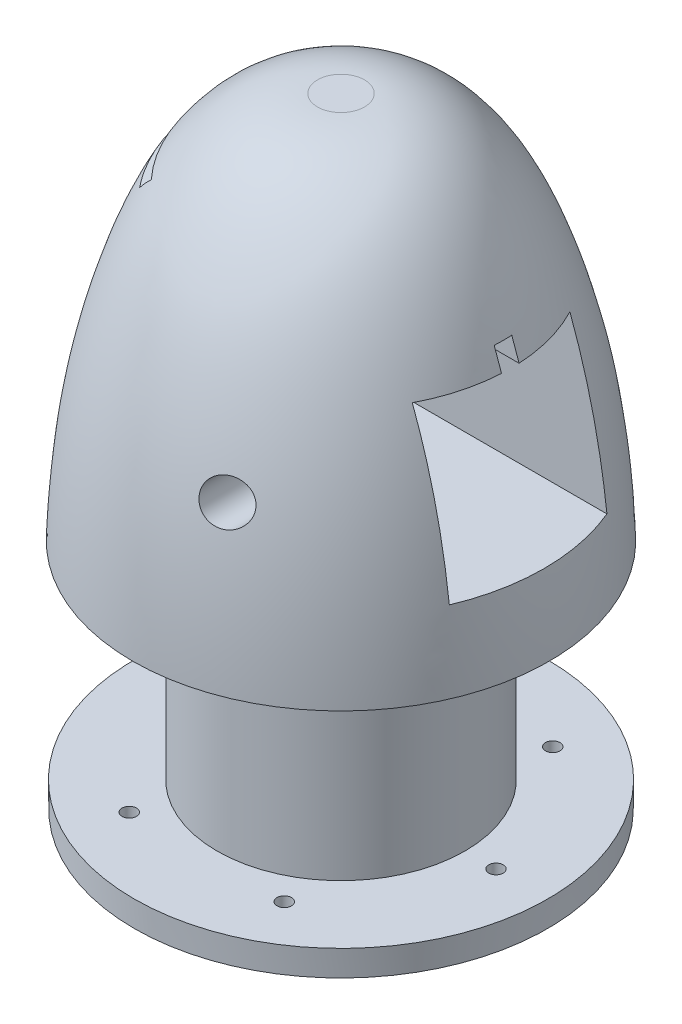
SolidWorks part; units mm, degrees
ref_plane "Front Plane" through (0, 0, 0) normal (0, 0, 1) x (1, 0, 0)
ref_plane "Top Plane" through (0, 0, 0) normal (0, 1, 0) x (1, 0, 0)
ref_plane "Right Plane" through (0, 0, 0) normal (1, 0, 0) x (0, 0, -1)
sketch "Sketch3" plane through (0, 0, 0) normal (1, 0, 0) x (0, 0, -1)
  line L0 (0, 0) -> (0, 152.4)
  line L9 (0, 152.4) -> (5.7751, 152.4)
  line L10 (0, 0) -> (50.8, 0)
  spline S0 degree 3 poles (5.7751, 152.4) (26.1046, 152.1019) (56.3315, 91.4598) (51.0277, 40.2864) (50.8, 0) knots 0 0 0 0 0.330383 1 1 1 1
  point P5 (5.7751, 152.4)
  dimension "D1" = 152.4
  dimension "D2" = 50.8
revolve "Revolve2" add sketch "Sketch3" angle 360 about L0
sketch "Sketch4" plane through (0, 0, 0) normal (1, 0, 0) x (0, 0, -1)
  line L0 (0, 0) -> (0, 109.601) construction
  line L1 (5.7751, 152.4) -> (-5.7751, 152.4) construction
  line L2 (-50.8, 0) -> (50.8, 0) construction
  line L3 (-19.3675, 114.681) -> (-2.159, 114.681)
  line L4 (-19.3675, 114.681) -> (-19.3675, 76.2)
  line L5 (-19.3675, 76.2) -> (19.3675, 76.2)
  line L6 (19.3675, 114.681) -> (19.3675, 76.2)
  line L7 (-19.3675, 114.681) -> (19.3675, 76.2) construction
  line L8 (-19.3675, 76.2) -> (19.3675, 114.681) construction
  line L9 (0, 114.681) -> (0, 152.4) construction
  line L11 (-2.159, 114.681) -> (-2.159, 119.761)
  line L12 (-2.159, 119.761) -> (2.159, 119.761)
  line L13 (2.159, 114.681) -> (2.159, 119.761)
  line L14 (0, 114.681) -> (2.159, 119.761) construction
  line L15 (-2.159, 119.761) -> (0, 114.681) construction
  line L16 (2.159, 114.681) -> (19.3675, 114.681)
  point P5 (0, 95.4405)
  point P12 (0, 114.681)
  point P14 (2.159, 117.221)
  point P16 (-2.159, 117.221)
  dimension "D1" = 2.159
  dimension "38.2mm" = 38.481
  dimension "D2" = 38.735
  dimension "D3" = 76.2
  dimension "D4" = 5.08
  dimension "D5" = 2.159
extrude "Cut-Extrude1" cut sketch "Sketch4" against normal blind 12.7 and the other way through all
sketch "Sketch5" plane through (0, 0, 0) normal (1, 0, 0) x (0, 0, -1)
  line L0 (0, 76.2) -> (0, 119.761) construction
  line L1 (-19.3675, 76.2) -> (19.3675, 76.2) construction
  line L2 (-2.159, 119.761) -> (2.159, 119.761) construction
  line L3 (-19.3675, 95.4405) -> (19.3675, 95.4405) construction
  line L4 (-19.3675, 114.681) -> (-19.3675, 76.2) construction
  line L5 (19.3675, 114.681) -> (19.3675, 76.2) construction
  circle A0 centre (0, 95.4405) radius 24.4446
  point P10 (0, 0)
extrude "Cut-Extrude2" cut sketch "Sketch5" against normal blind 66.04
sketch "Sketch10" plane through (0, 0, 0) normal (0, 0, 1) x (1, 0, 0)
  circle A0 centre (15.8964, 95.3) radius 3.175 construction
  circle A1 centre (15.8964, 95.3) radius 3.175
extrude "Cut-Extrude3" cut sketch "Sketch10" against normal through all both and the other way through all
sketch "Sketch12" plane through (0, 0, 22.86) normal (0, 0, 1) x (1, 0, 0)
  circle A0 centre (15.8964, 95.3) radius 5.08
  dimension "D1" = 10.16
extrude "Cut-Extrude4" cut sketch "Sketch12" along normal blind 43.688 and the other way blind 0.508
sketch "Sketch13" plane through (0, 0, -22.86) normal (0, 0, 1) x (1, 0, 0)
  circle A0 centre (15.8964, 95.3) radius 5.08
  dimension "D1" = 10.16
extrude "Cut-Extrude5" cut sketch "Sketch13" against normal blind 43.688
sketch "Sketch16" plane through (0, 0, 0) normal (0, -1, 0) x (1, 0, 0)
  circle A0 centre (0, 0) radius 38.1 construction
  circle A7 centre (38.1, 0) radius 1.778
  circle A8 centre (19.05, -32.9956) radius 1.778
  circle A9 centre (-19.05, -32.9956) radius 1.778
  circle A10 centre (-38.1, 0) radius 1.778
  circle A11 centre (-19.05, 32.9956) radius 1.778
  circle A12 centre (19.05, 32.9956) radius 1.778
  point P12 (0, 0)
  point P18 (0, 0)
  dimension "D1" = 76.2
  dimension "D2" = 3.556
  dimension "D3" = 6
sketch "Sketch19" plane through (0, 0, 0) normal (0, 0, 1) x (1, 0, 0)
  line L0 (0, 0) -> (0, 72.1255) construction
  line L1 (-38.1, 0) -> (38.1, 0) construction
  line L2 (30.48, 57.15) -> (105.1025, 57.15)
  line L3 (30.48, 57.15) -> (30.48, 6.35)
  line L4 (30.48, 6.35) -> (105.1025, 6.35)
  line L5 (105.1025, 57.15) -> (105.1025, 6.35)
  dimension "D1" = 6.35
  dimension "D2" = 50.8
  dimension "D3" = 30.48
revolve "Cut-Revolve1" cut sketch "Sketch19" angle 360 about L0
extrude "Cut-Extrude6" cut sketch "Sketch16" against normal blind 7.62
ref_plane "Plane1" through (-35.56, 0, 0) normal (-1, 0, 0) x (0, 0, 1)
sketch "Sketch20" plane through (-35.56, 0, 0) normal (-1, 0, 0) x (0, 0, 1)
  line L0 (23.0222, 130.6485) -> (1.7963, 133.35)
  line L1 (2.0378, 137.16) -> (23.6815, 134.4053)
  line L2 (-1.7963, 133.35) -> (-23.0222, 130.6485)
  line L3 (-23.6815, 134.4053) -> (-2.0378, 137.16)
  line L4 (1.7963, 133.35) -> (-1.7963, 133.35)
  line L5 (-2.0378, 137.16) -> (2.0378, 137.16)
  line L6 (-23.6815, 134.4053) -> (-23.0222, 130.6485)
  line L7 (23.6815, 134.4053) -> (23.0222, 130.6485)
  line L8 (0, 0) -> (0, 204.5903) construction
  point P8 (0, 133.35)
  point P12 (0, 0)
  dimension "D1" = 133.35
extrude "Cut-Extrude7" cut sketch "Sketch20" against normal blind 19.05
